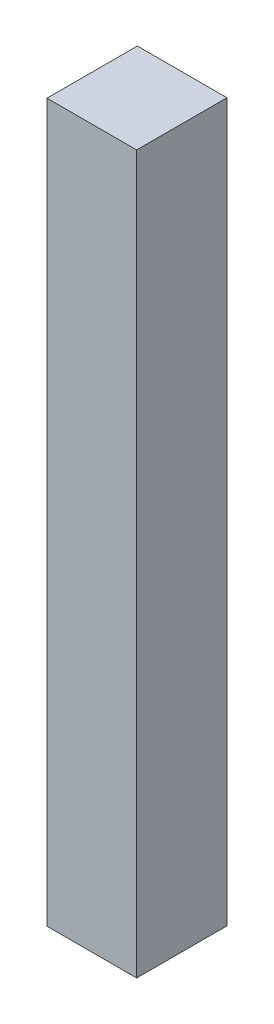
SolidWorks part; units mm, degrees
ref_plane "Front Plane" through (0, 0, 0) normal (0, 0, 1) x (1, 0, 0)
ref_plane "Top Plane" through (0, 0, 0) normal (0, 1, 0) x (1, 0, 0)
ref_plane "Right Plane" through (0, 0, 0) normal (1, 0, 0) x (0, 0, -1)
sketch "Sketch1" plane through (0, 0, 0) normal (0, 1, 0) x (1, 0, 0)
  line L1 (0, 0) -> (3.175, 0)
  line L2 (0, 0) -> (0, 3.2004)
  line L3 (0, 3.2004) -> (3.175, 3.2004)
  line L4 (3.175, 0) -> (3.175, 3.2004)
extrude "Boss-Extrude1" add sketch "Sketch1" along normal blind 25.4
